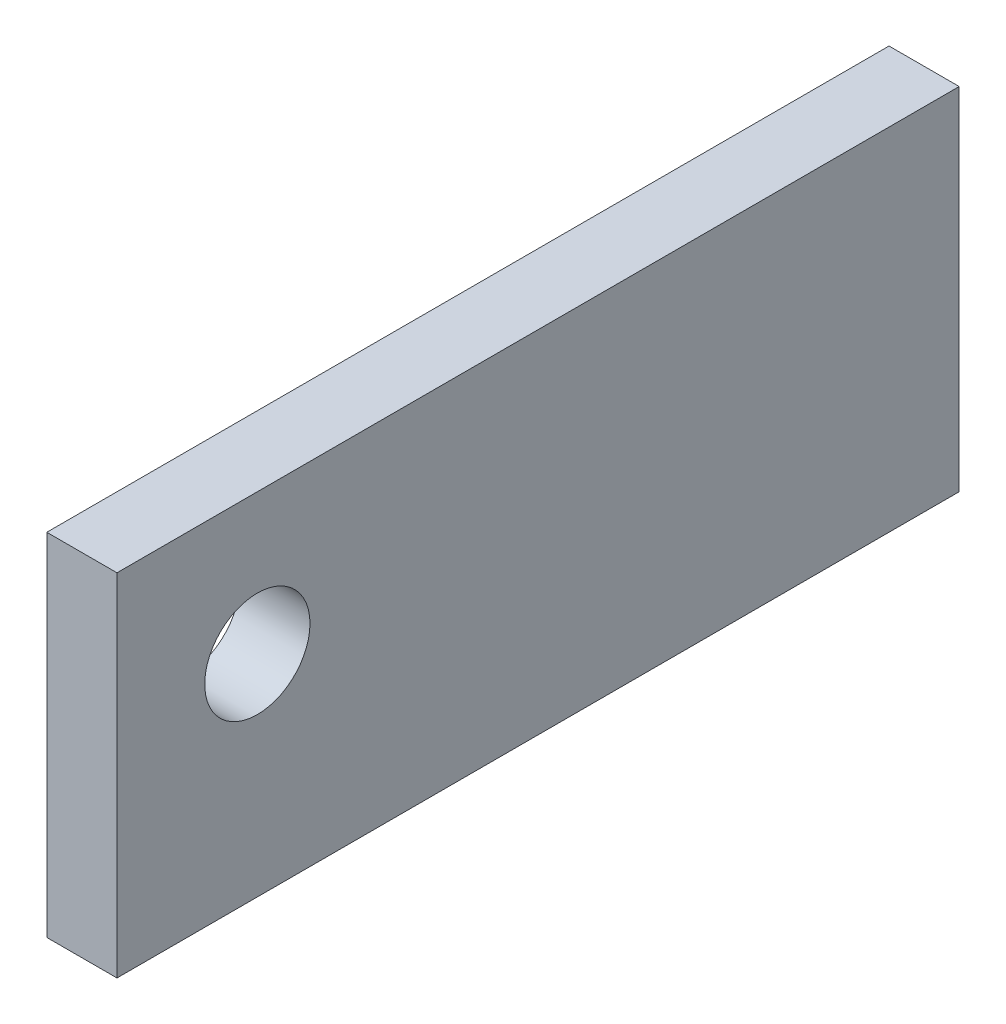
SolidWorks part; units mm, degrees
ref_plane "Front Plane" through (0, 0, 0) normal (0, 0, 1) x (1, 0, 0)
ref_plane "Top Plane" through (0, 0, 0) normal (0, 1, 0) x (1, 0, 0)
ref_plane "Right Plane" through (0, 0, 0) normal (1, 0, 0) x (0, 0, -1)
sketch "Sketch1" plane through (0, 0, 0) normal (1, 0, 0) x (0, 0, -1)
  line L1 (-76.2, 31.75) -> (76.2, 31.75)
  line L2 (-76.2, 31.75) -> (-76.2, -31.75)
  line L3 (-76.2, -31.75) -> (76.2, -31.75)
  line L4 (76.2, 31.75) -> (76.2, -31.75)
  line L5 (-76.2, 31.75) -> (76.2, -31.75) construction
  line L6 (-76.2, -31.75) -> (76.2, 31.75) construction
  point P0 (0, 0)
  dimension "D1" = 63.5
  dimension "D2" = 152.4
extrude "Boss-Extrude1" add sketch "Sketch1" along normal mid plane 12.7
sketch "Sketch2" plane through (6.35, 0, 0) normal (1, 0, 0) x (0, 0, -1)
  line L0 (76.2, 31.75) -> (-76.2, 31.75) construction
  line L2 (-76.2, 31.75) -> (-76.2, -31.75) construction
  circle A0 centre (-50.8, 6.35) radius 9.525
  dimension "D1" = 19.05
  dimension "D2" = 25.4
  dimension "D3" = 25.4
extrude "Cut-Extrude1" cut sketch "Sketch2" against normal up to next
sketch "Sketch3" plane through (0, 0, -76.2) normal (0, 0, -1) x (-1, 0, 0)
  line L0 (0, 31.75) -> (0, -31.75) construction
  line L1 (-6.35, 31.75) -> (6.35, 31.75) construction
  line L2 (-6.35, -31.75) -> (6.35, -31.75) construction
  line L3 (-6.35, 0) -> (6.35, 0) construction
  line L4 (-6.35, -31.75) -> (-6.35, 31.75) construction
  line L5 (6.35, -31.75) -> (6.35, 31.75) construction
